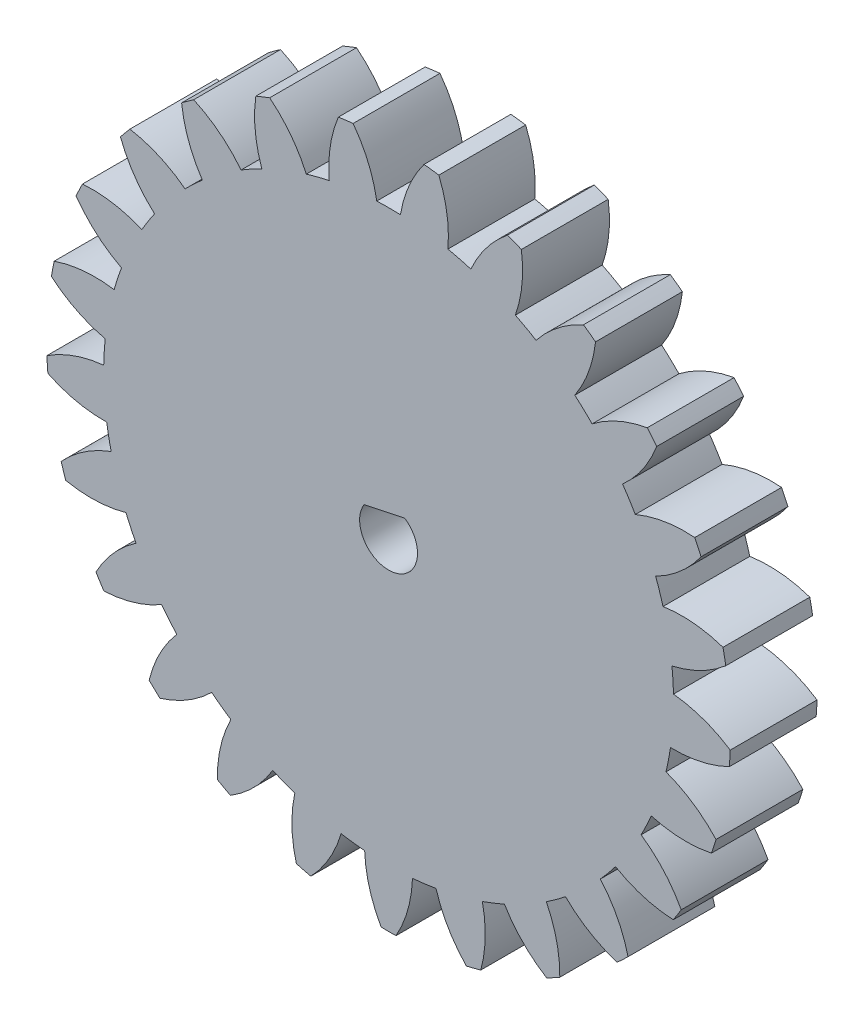
SolidWorks part; units mm, degrees
ref_plane "Front Plane" through (0, 0, 0) normal (0, 0, 1) x (1, 0, 0)
ref_plane "Top Plane" through (0, 0, 0) normal (0, 1, 0) x (1, 0, 0)
ref_plane "Right Plane" through (0, 0, 0) normal (1, 0, 0) x (0, 0, -1)
sketch "Sketch1" plane through (0, 0, 0) normal (0, 0, 1) x (1, 0, 0)
  arc A0 (-23.2975, 3.9839) -> (-19.5792, 2.1161) centre (-17.6233, 10.6447) ccw
  arc A1 (-19.5792, 2.1161) -> (-19.6821, 0.4813) centre (0, 0.0637) ccw
  arc A2 (-19.6821, 0.4813) -> (-23.6051, -0.9057) centre (-18.8105, -8.2251) ccw
  arc A3 (-23.6051, -0.9057) -> (-23.5405, -1.9331) centre (0, 0.0637) ccw
  arc A4 (-23.5405, -1.9331) -> (-19.4745, -2.8175) centre (-19.7011, 5.9295) ccw
  arc A5 (-19.4745, -2.8175) -> (-19.1676, -4.4265) centre (0, 0.0637) ccw
  arc A6 (-19.1676, -4.4265) -> (-22.6224, -6.7456) centre (-16.1582, -12.6427) ccw
  arc A7 (-22.6224, -6.7456) -> (-22.3043, -7.7247) centre (0, 0.0637) ccw
  arc A8 (-22.3043, -7.7247) -> (-18.1462, -7.5701) centre (-20.5409, 0.8458) ccw
  arc A9 (-18.1462, -7.5701) -> (-17.4487, -9.0522) centre (0, 0.0637) ccw
  arc A10 (-17.4487, -9.0522) -> (-20.2183, -12.1576) centre (-12.4906, -16.2619) ccw
  arc A11 (-20.2183, -12.1576) -> (-19.6667, -13.0268) centre (0, 0.0637) ccw
  arc A12 (-19.6667, -13.0268) -> (-15.6776, -11.8431) centre (-20.0901, -4.2871) ccw
  arc A13 (-15.6776, -11.8431) -> (-14.6335, -13.1052) centre (0, 0.0637) ccw
  arc A14 (-14.6335, -13.1052) -> (-16.5438, -16.8018) centre (-8.0382, -18.8553) ccw
  arc A15 (-16.5438, -16.8018) -> (-15.7934, -17.5065) centre (0, 0.0637) ccw
  arc A16 (-15.7934, -17.5065) -> (-12.224, -15.3679) centre (-18.3769, -9.1466) ccw
  arc A17 (-12.224, -15.3679) -> (-10.8988, -16.3306) centre (0, 0.0637) ccw
  arc A18 (-10.8988, -16.3306) -> (-11.8298, -20.3862) centre (-3.0807, -20.2599) ccw
  arc A19 (-11.8298, -20.3862) -> (-10.9277, -20.8821) centre (0, 0.0637) ccw
  arc A20 (-10.9277, -20.8821) -> (-8.0023, -17.923) centre (-15.5091, -13.4274) ccw
  arc A21 (-8.0023, -17.923) -> (-6.4793, -18.526) centre (0, 0.0637) ccw
  arc A22 (-6.4793, -18.526) -> (-6.3725, -22.6857) centre (2.0704, -20.3876) ccw
  arc A23 (-6.3725, -22.6857) -> (-5.3753, -22.9417) centre (0, 0.0637) ccw
  arc A24 (-5.3753, -22.9417) -> (-3.2778, -19.348) centre (-11.6667, -16.8605) ccw
  arc A25 (-3.2778, -19.348) -> (-1.6527, -19.5533) centre (0, 0.0637) ccw
  arc A26 (-1.6527, -19.5533) -> (-0.5147, -23.5557) centre (7.0913, -19.2302) ccw
  arc A27 (-0.5147, -23.5557) -> (0.5147, -23.5557) centre (0, 0.0637) ccw
  arc A28 (0.5147, -23.5557) -> (1.6527, -19.5533) centre (-7.0913, -19.2302) ccw
  arc A29 (1.6527, -19.5533) -> (3.2778, -19.348) centre (0, 0.0637) ccw
  arc A30 (3.2778, -19.348) -> (5.3753, -22.9417) centre (11.6667, -16.8605) ccw
  arc A31 (5.3753, -22.9417) -> (6.3725, -22.6857) centre (0, 0.0637) ccw
  arc A32 (6.3725, -22.6857) -> (6.4793, -18.526) centre (-2.0704, -20.3876) ccw
  arc A33 (6.4793, -18.526) -> (8.0023, -17.923) centre (0, 0.0637) ccw
  arc A34 (8.0023, -17.923) -> (10.9277, -20.8821) centre (15.5091, -13.4274) ccw
  arc A35 (10.9277, -20.8821) -> (11.8298, -20.3862) centre (0, 0.0637) ccw
  arc A36 (11.8298, -20.3862) -> (10.8988, -16.3306) centre (3.0807, -20.2599) ccw
  arc A37 (10.8988, -16.3306) -> (12.224, -15.3679) centre (0, 0.0637) ccw
  arc A38 (12.224, -15.3679) -> (15.7934, -17.5065) centre (18.3769, -9.1466) ccw
  arc A39 (15.7934, -17.5065) -> (16.5438, -16.8018) centre (0, 0.0637) ccw
  arc A40 (16.5438, -16.8018) -> (14.6335, -13.1052) centre (8.0382, -18.8553) ccw
  arc A41 (14.6335, -13.1052) -> (15.6776, -11.8431) centre (0, 0.0637) ccw
  arc A42 (15.6776, -11.8431) -> (19.6667, -13.0268) centre (20.0901, -4.2871) ccw
  arc A43 (19.6667, -13.0268) -> (20.2183, -12.1576) centre (0, 0.0637) ccw
  arc A44 (20.2183, -12.1576) -> (17.4487, -9.0522) centre (12.4906, -16.2619) ccw
  arc A45 (17.4487, -9.0522) -> (18.1462, -7.5701) centre (0, 0.0637) ccw
  arc A46 (18.1462, -7.5701) -> (22.3043, -7.7247) centre (20.5409, 0.8458) ccw
  arc A47 (22.3043, -7.7247) -> (22.6224, -6.7456) centre (0, 0.0637) ccw
  arc A48 (22.6224, -6.7456) -> (19.1676, -4.4265) centre (16.1582, -12.6427) ccw
  arc A49 (19.1676, -4.4265) -> (19.4745, -2.8175) centre (0, 0.0637) ccw
  arc A50 (19.4745, -2.8175) -> (23.5405, -1.9331) centre (19.7011, 5.9295) ccw
  arc A51 (23.5405, -1.9331) -> (23.6051, -0.9057) centre (0, 0.0637) ccw
  arc A52 (23.6051, -0.9057) -> (19.6821, 0.4813) centre (18.8105, -8.2251) ccw
  arc A53 (19.6821, 0.4813) -> (19.5792, 2.1161) centre (0, 0.0637) ccw
  arc A54 (19.5792, 2.1161) -> (23.2975, 3.9839) centre (17.6233, 10.6447) ccw
  arc A55 (23.2975, 3.9839) -> (23.1046, 4.9951) centre (0, 0.0637) ccw
  arc A56 (23.1046, 4.9951) -> (18.9598, 5.363) centre (20.2809, -3.2867) ccw
  arc A57 (18.9598, 5.363) -> (18.4537, 6.9208) centre (0, 0.0637) ccw
  arc A58 (18.4537, 6.9208) -> (21.5906, 9.6546) centre (14.4383, 14.695) ccw
  arc A59 (21.5906, 9.6546) -> (21.1523, 10.5861) centre (0, 0.0637) ccw
  arc A60 (21.1523, 10.5861) -> (17.0463, 9.9116) centre (20.4769, 1.8622) ccw
  arc A61 (17.0463, 9.9116) -> (16.1686, 11.2946) centre (0, 0.0637) ccw
  arc A62 (16.1686, 11.2946) -> (18.5272, 14.7226) centre (10.346, 17.826) ccw
  arc A63 (18.5272, 14.7226) -> (17.871, 15.5158) centre (0, 0.0637) ccw
  arc A64 (17.871, 15.5158) -> (14.0617, 13.8414) centre (19.3864, 6.8981) ccw
  arc A65 (14.0617, 13.8414) -> (12.8676, 14.9627) centre (0, 0.0637) ccw
  arc A66 (12.8676, 14.9627) -> (14.2996, 18.8696) centre (5.6036, 19.8409) ccw
  arc A67 (14.2996, 18.8696) -> (13.4667, 19.4747) centre (0, 0.0637) ccw
  arc A68 (13.4667, 19.4747) -> (10.1935, 16.9056) centre (17.0777, 11.5045) ccw
  arc A69 (10.1935, 16.9056) -> (8.7581, 17.6947) centre (0, 0.0637) ccw
  arc A70 (8.7581, 17.6947) -> (9.1735, 21.8349) centre (0.5092, 20.6131) ccw
  arc A71 (9.1735, 21.8349) -> (8.2163, 22.2139) centre (0, 0.0637) ccw
  arc A72 (8.2163, 22.2139) -> (5.6849, 18.9115) centre (13.6959, 15.3922) ccw
  arc A73 (5.6849, 18.9115) -> (4.0983, 19.3189) centre (0, 0.0637) ccw
  arc A74 (4.0983, 19.3189) -> (3.471, 23.4323) centre (-4.6173, 20.0942) ccw
  arc A75 (3.471, 23.4323) -> (2.4496, 23.5613) centre (0, 0.0637) ccw
  arc A76 (2.4496, 23.5613) -> (0.819, 19.7331) centre (9.4536, 18.3166) ccw
  arc A77 (0.819, 19.7331) -> (-0.819, 19.7331) centre (0, 0.0637) ccw
  arc A78 (-0.819, 19.7331) -> (-2.4496, 23.5613) centre (-9.4536, 18.3166) ccw
  arc A79 (-2.4496, 23.5613) -> (-3.471, 23.4323) centre (0, 0.0637) ccw
  arc A80 (-3.471, 23.4323) -> (-4.0983, 19.3189) centre (4.6173, 20.0942) ccw
  arc A81 (-4.0983, 19.3189) -> (-5.6849, 18.9115) centre (0, 0.0637) ccw
  arc A82 (-5.6849, 18.9115) -> (-8.2163, 22.2139) centre (-13.6959, 15.3922) ccw
  arc A83 (-8.2163, 22.2139) -> (-9.1735, 21.8349) centre (0, 0.0637) ccw
  arc A84 (-9.1735, 21.8349) -> (-8.7581, 17.6947) centre (-0.5092, 20.6131) ccw
  arc A85 (-8.7581, 17.6947) -> (-10.1935, 16.9056) centre (0, 0.0637) ccw
  arc A86 (-10.1935, 16.9056) -> (-13.4667, 19.4747) centre (-17.0777, 11.5045) ccw
  arc A87 (-13.4667, 19.4747) -> (-14.2996, 18.8696) centre (0, 0.0637) ccw
  arc A88 (-14.2996, 18.8696) -> (-12.8676, 14.9627) centre (-5.6036, 19.8409) ccw
  arc A89 (-12.8676, 14.9627) -> (-14.0617, 13.8414) centre (0, 0.0637) ccw
  arc A90 (-14.0617, 13.8414) -> (-17.871, 15.5158) centre (-19.3864, 6.8981) ccw
  arc A91 (-17.871, 15.5158) -> (-18.5272, 14.7226) centre (0, 0.0637) ccw
  arc A92 (-18.5272, 14.7226) -> (-16.1686, 11.2946) centre (-10.346, 17.826) ccw
  arc A93 (-16.1686, 11.2946) -> (-17.0463, 9.9116) centre (0, 0.0637) ccw
  arc A94 (-17.0463, 9.9116) -> (-21.1523, 10.5861) centre (-20.4769, 1.8622) ccw
  arc A95 (-21.1523, 10.5861) -> (-21.5906, 9.6546) centre (0, 0.0637) ccw
  arc A96 (-21.5906, 9.6546) -> (-18.4537, 6.9208) centre (-14.4383, 14.695) ccw
  arc A97 (-18.4537, 6.9208) -> (-18.9598, 5.363) centre (0, 0.0637) ccw
  arc A98 (-18.9598, 5.363) -> (-23.1046, 4.9951) centre (-20.2809, -3.2867) ccw
  arc A99 (-23.1046, 4.9951) -> (-23.2975, 3.9839) centre (0, 0.0637) ccw
extrude "Boss-Extrude1" add sketch "Sketch1" along normal blind 6
sketch "Sketch2" plane through (0, 0, 6) normal (0, 0, 1) x (1, 0, 0)
  line L0 (-1.6879, 1.1365) -> (1.1064, 1.7298)
  arc A0 (-1.6879, 1.1365) -> (1.1064, 1.7298) centre (0, 0.0637) ccw
  arc A1 (-1.6879, 1.1365) -> (1.1064, 1.7298) centre (0, 0.0637) ccw construction
extrude "Cut-Extrude1" cut sketch "Sketch2" against normal blind 6
